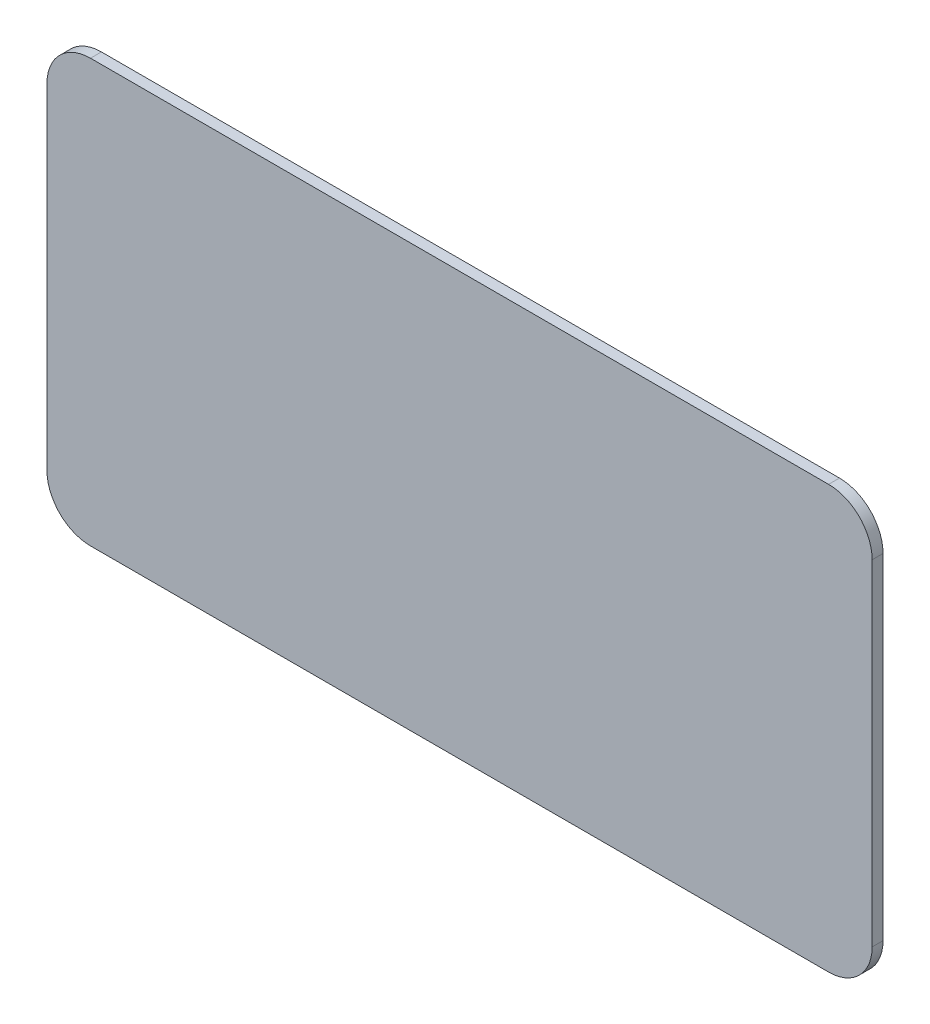
SolidWorks part; units mm, degrees
ref_plane "前视基准面" through (0, 0, 0) normal (0, 0, 1) x (1, 0, 0)
ref_plane "上视基准面" through (0, 0, 0) normal (0, 1, 0) x (1, 0, 0)
ref_plane "右视基准面" through (0, 0, 0) normal (1, 0, 0) x (0, 0, -1)
sketch "草图1" plane through (0, 0, 0) normal (0, 0, 1) x (1, 0, 0)
  line L1 (0, 0) -> (758, 0)
  line L2 (0, 0) -> (0, 388)
  line L3 (0, 388) -> (758, 388)
  line L4 (758, 0) -> (758, 388)
extrude "凸台-拉伸1" add sketch "草图1" along normal blind 10
fillet "圆角1" radius 40 1 edges at (758, 388, 5)
fillet "圆角2" radius 40 1 edges at (758, 0, 5)
fillet "圆角3" radius 40 1 edges at (0, 0, 5)
fillet "圆角4" radius 40 1 edges at (0, 388, 5)
sketch "草图3" [suppressed] plane through (0, 0, 10) normal (0, 0, 1) x (1, 0, 0)
  line L0 (260, 388) -> (260, 0)
  line L2 (498, 388) -> (498, 0)
  line L3 (718, 388) -> (40, 388) construction
  line L4 (498, 388) -> (496, 388)
  line L5 (496, 388) -> (496, 0)
  line L6 (40, 0) -> (718, 0) construction
  line L7 (496, 0) -> (498, 0)
  line L10 (262, 0) -> (260, 0)
  line L11 (262, 388) -> (262, 0)
  line L12 (260, 388) -> (262, 388)
